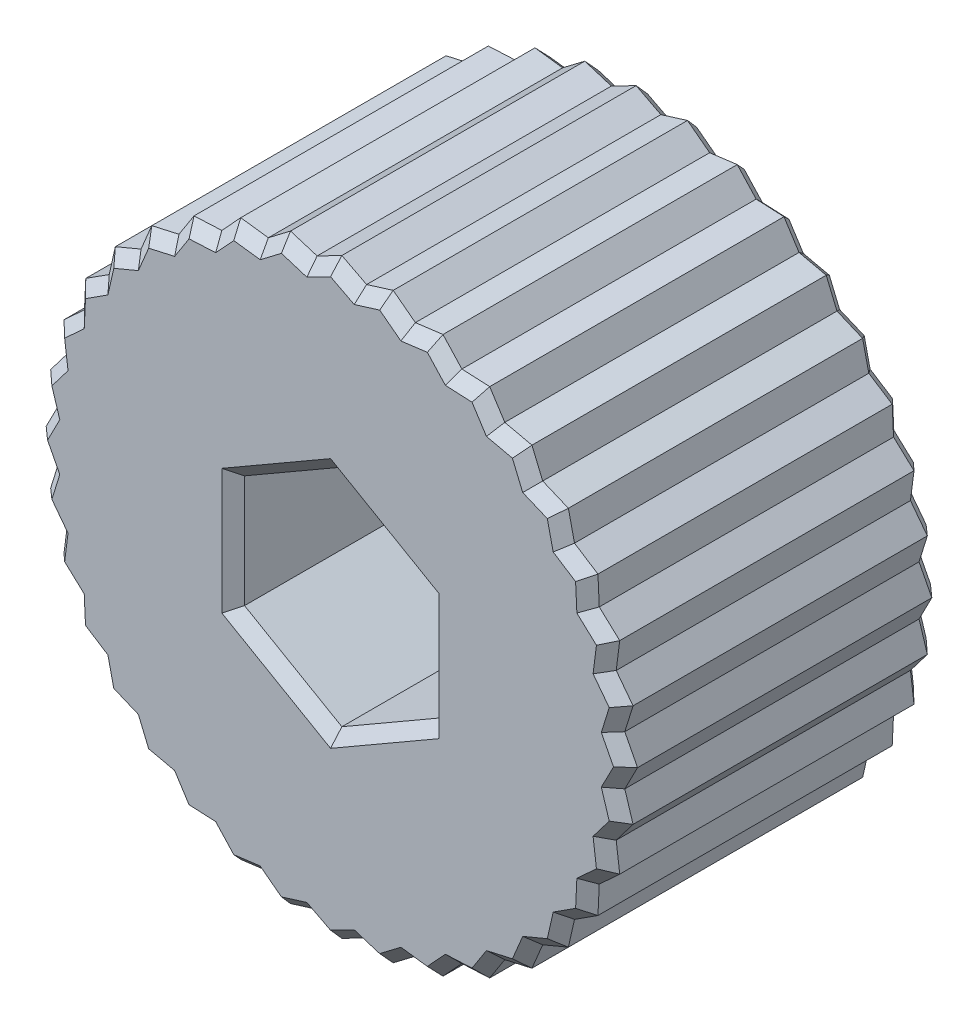
SolidWorks part; units mm, degrees
ref_plane "Front Plane (Z)" through (0, 0, 0) normal (0, 0, 1) x (1, 0, 0)
ref_plane "Top Plane (Y)" through (0, 0, 0) normal (0, 1, 0) x (1, 0, 0)
ref_plane "Side Plane (X)" through (0, 0, 0) normal (1, 0, 0) x (0, 0, -1)
sketch "Sketch1" plane through (0, 0, 0) normal (0, 0, 1) x (1, 0, 0)
  line L1 (0, 4.6765) -> (-4.05, 2.3383)
  line L2 (-4.05, 2.3383) -> (-4.05, -2.3383)
  line L3 (-4.05, -2.3383) -> (0, -4.6765)
  line L4 (0, -4.6765) -> (4.05, -2.3383)
  line L5 (4.05, -2.3383) -> (4.05, 2.3383)
  line L6 (4.05, 2.3383) -> (0, 4.6765)
  circle A1 centre (0, 0) radius 12.5
  circle A2 centre (0, 0) radius 4.05 construction
  dimension "D1" = 8.1
  dimension "D2" = 25
extrude "Boss-Extrude1" add sketch "Sketch1" along normal blind 14
sketch "Sketch3" plane through (0, 0, 0) normal (0, 0, -1) x (-1, 0, 0)
  circle A0 centre (0, 0) radius 2.9
  circle A1 centre (0, 0) radius 5.8015
  dimension "D1" = 5.8
extrude "Boss-Extrude3" add sketch "Sketch3" against normal blind 2
sketch "Sketch4" plane through (0, 0, 14) normal (0, 0, 1) x (1, 0, 0)
  line L0 (4.05, 2.3383) -> (4.05, -2.3383) construction
  line L1 (0, 4.9652) -> (-4.3, 2.4826)
  line L2 (-4.3, 2.4826) -> (-4.3, -2.4826)
  line L3 (-4.3, -2.4826) -> (0, -4.9652)
  line L4 (0, -4.9652) -> (4.3, -2.4826)
  line L5 (4.3, -2.4826) -> (4.3, 2.4826)
  line L6 (4.3, 2.4826) -> (0, 4.9652)
  circle A0 centre (0, 0) radius 4.3 construction
  dimension "D1" = 0.25
extrude "Cut-Extrude1" cut sketch "Sketch4" against normal offset from surface (7.5 mm away) 4.5 up to face at (0, 0, 2)
sketch "Sketch5" plane through (0, 0, 14) normal (0, 0, 1) x (1, 0, 0)
  line L0 (0, 0) -> (0, 15.5343) construction
  line L1 (0, 13.0632) -> (1.0936, 12.4995)
  line L2 (0, 0) -> (1.0936, 12.4995) construction
  line L3 (0, 13.0632) -> (-1.0936, 12.4995)
  line L4 (2.2684, 12.8647) -> (1.0936, 12.4995)
  line L5 (2.2684, 12.8647) -> (3.2475, 12.1197)
  line L6 (4.4679, 12.2754) -> (3.2475, 12.1197)
  line L7 (4.4679, 12.2754) -> (5.3027, 11.3716)
  line L8 (6.5316, 11.3131) -> (5.3027, 11.3716)
  line L9 (6.5316, 11.3131) -> (7.1968, 10.2781)
  line L10 (8.3969, 10.007) -> (7.1968, 10.2781)
  line L11 (8.3969, 10.007) -> (8.8722, 8.8722)
  line L12 (10.007, 8.3969) -> (8.8722, 8.8722)
  line L13 (10.007, 8.3969) -> (10.2781, 7.1968)
  line L14 (11.3131, 6.5316) -> (10.2781, 7.1968)
  line L15 (11.3131, 6.5316) -> (11.3716, 5.3027)
  line L16 (12.2754, 4.4679) -> (11.3716, 5.3027)
  line L17 (12.2754, 4.4679) -> (12.1197, 3.2475)
  line L18 (12.8647, 2.2684) -> (12.1197, 3.2475)
  line L19 (12.8647, 2.2684) -> (12.4995, 1.0936)
  line L20 (13.0632, 0) -> (12.4995, 1.0936)
  line L21 (13.0632, 0) -> (12.4995, -1.0936)
  line L22 (12.8647, -2.2684) -> (12.4995, -1.0936)
  line L23 (12.8647, -2.2684) -> (12.1197, -3.2475)
  line L24 (12.2754, -4.4679) -> (12.1197, -3.2475)
  line L25 (12.2754, -4.4679) -> (11.3716, -5.3027)
  line L26 (11.3131, -6.5316) -> (11.3716, -5.3027)
  line L27 (11.3131, -6.5316) -> (10.2781, -7.1968)
  line L28 (10.007, -8.3969) -> (10.2781, -7.1968)
  line L29 (10.007, -8.3969) -> (8.8722, -8.8722)
  line L30 (8.3969, -10.007) -> (8.8722, -8.8722)
  line L31 (8.3969, -10.007) -> (7.1968, -10.2781)
  line L32 (6.5316, -11.3131) -> (7.1968, -10.2781)
  line L33 (6.5316, -11.3131) -> (5.3027, -11.3716)
  line L34 (4.4679, -12.2754) -> (5.3027, -11.3716)
  line L35 (4.4679, -12.2754) -> (3.2475, -12.1197)
  line L36 (2.2684, -12.8647) -> (3.2475, -12.1197)
  line L37 (2.2684, -12.8647) -> (1.0936, -12.4995)
  line L38 (0, -13.0632) -> (1.0936, -12.4995)
  line L39 (0, -13.0632) -> (-1.0936, -12.4995)
  line L40 (-2.2684, -12.8647) -> (-1.0936, -12.4995)
  line L41 (-2.2684, -12.8647) -> (-3.2475, -12.1197)
  line L42 (-4.4679, -12.2754) -> (-3.2475, -12.1197)
  line L43 (-4.4679, -12.2754) -> (-5.3027, -11.3716)
  line L44 (-6.5316, -11.3131) -> (-5.3027, -11.3716)
  line L45 (-6.5316, -11.3131) -> (-7.1968, -10.2781)
  line L46 (-8.3969, -10.007) -> (-7.1968, -10.2781)
  line L47 (-8.3969, -10.007) -> (-8.8722, -8.8722)
  line L48 (-10.007, -8.3969) -> (-8.8722, -8.8722)
  line L49 (-10.007, -8.3969) -> (-10.2781, -7.1968)
  line L50 (-11.3131, -6.5316) -> (-10.2781, -7.1968)
  line L51 (-11.3131, -6.5316) -> (-11.3716, -5.3027)
  line L52 (-12.2754, -4.4679) -> (-11.3716, -5.3027)
  line L53 (-12.2754, -4.4679) -> (-12.1197, -3.2475)
  line L54 (-12.8647, -2.2684) -> (-12.1197, -3.2475)
  line L55 (-12.8647, -2.2684) -> (-12.4995, -1.0936)
  line L56 (-13.0632, 0) -> (-12.4995, -1.0936)
  line L57 (-13.0632, 0) -> (-12.4995, 1.0936)
  line L58 (-12.8647, 2.2684) -> (-12.4995, 1.0936)
  line L59 (-12.8647, 2.2684) -> (-12.1197, 3.2475)
  line L60 (-12.2754, 4.4679) -> (-12.1197, 3.2475)
  line L61 (-12.2754, 4.4679) -> (-11.3716, 5.3027)
  line L62 (-11.3131, 6.5316) -> (-11.3716, 5.3027)
  line L63 (-11.3131, 6.5316) -> (-10.2781, 7.1968)
  line L64 (-10.007, 8.3969) -> (-10.2781, 7.1968)
  line L65 (-10.007, 8.3969) -> (-8.8722, 8.8722)
  line L66 (-8.3969, 10.007) -> (-8.8722, 8.8722)
  line L67 (-8.3969, 10.007) -> (-7.1968, 10.2781)
  line L68 (-6.5316, 11.3131) -> (-7.1968, 10.2781)
  line L69 (-6.5316, 11.3131) -> (-5.3027, 11.3716)
  line L70 (-4.4679, 12.2754) -> (-5.3027, 11.3716)
  line L71 (-4.4679, 12.2754) -> (-3.2475, 12.1197)
  line L72 (-2.2684, 12.8647) -> (-3.2475, 12.1197)
  line L73 (-2.2684, 12.8647) -> (-1.0936, 12.4995)
  circle A1 centre (0, 0) radius 12.0902
  point P115 (0, 0)
  dimension "D2" = 36
extrude "Boss-Extrude4" add sketch "Sketch5" against normal up to surface (14 mm away) up to face at (12.5, 0, 0)
chamfer "Chamfer2" distance 0.5 angle 45 151 edges at (-2.9, 0, 0) (-4.3, 0, 14) (-2.15, -3.7239, 14) (2.15, -3.7239, 14) (4.3, 0, 14) (2.15, 3.7239, 14) (-2.15, 3.7239, 14) (-1.681, 12.6821, 0) (-1.681, 12.6821, 14) (-2.7579, 12.4922, 0) (-2.7579, 12.4922, 14) (-3.8577, 12.1975, 0) (-3.8577, 12.1975, 14) (-4.8853, 11.8235, 0) (-4.8853, 11.8235, 14) (-5.9171, 11.3424, 0) (-5.9171, 11.3424, 14) (-6.8642, 10.7956, 0) (-6.8642, 10.7956, 14) (-7.7968, 10.1425, 0) (-7.7968, 10.1425, 14) (-8.6345, 9.4396, 0) (-8.6345, 9.4396, 14) (-9.4396, 8.6345, 0) (-9.4396, 8.6345, 14) (-10.1425, 7.7968, 0) (-10.1425, 7.7968, 14) (-10.7956, 6.8642, 0) (-10.7956, 6.8642, 14) (-11.3424, 5.9171, 0) (-11.3424, 5.9171, 14) (-11.8235, 4.8853, 0) (-11.8235, 4.8853, 14) (-12.1975, 3.8577, 0) (-12.1975, 3.8577, 14) (-12.4922, 2.7579, 0) (-12.4922, 2.7579, 14) (-12.6821, 1.681, 0) (-12.6821, 1.681, 14) (-12.7813, 0.5468, 0) (-12.7813, 0.5468, 14) (-12.7813, -0.5468, 0) (-12.7813, -0.5468, 14) (-12.6821, -1.681, 0) (-12.6821, -1.681, 14) (-12.4922, -2.7579, 0) (-12.4922, -2.7579, 14) (-12.1975, -3.8577, 0) (-12.1975, -3.8577, 14) (-11.8235, -4.8853, 0) (-11.8235, -4.8853, 14) (-11.3424, -5.9171, 0) (-11.3424, -5.9171, 14) (-10.7956, -6.8642, 0) (-10.7956, -6.8642, 14) (-10.1425, -7.7968, 0) (-10.1425, -7.7968, 14) (-9.4396, -8.6345, 0) (-9.4396, -8.6345, 14) (-8.6345, -9.4396, 0) (-8.6345, -9.4396, 14) (-7.7968, -10.1425, 0) (-7.7968, -10.1425, 14) (-6.8642, -10.7956, 0) (-6.8642, -10.7956, 14) (-5.9171, -11.3424, 0) (-5.9171, -11.3424, 14) (-4.8853, -11.8235, 0) (-4.8853, -11.8235, 14) (-3.8577, -12.1975, 0) (-3.8577, -12.1975, 14) (-2.7579, -12.4922, 0) (-2.7579, -12.4922, 14) (-1.681, -12.6821, 0) (-1.681, -12.6821, 14) (-0.5468, -12.7813, 0) (-0.5468, -12.7813, 14) (0.5468, -12.7813, 0) (0.5468, -12.7813, 14) (1.681, -12.6821, 0) (1.681, -12.6821, 14) (2.7579, -12.4922, 0) (2.7579, -12.4922, 14) (3.8577, -12.1975, 0) (3.8577, -12.1975, 14) (4.8853, -11.8235, 0) (4.8853, -11.8235, 14) (5.9171, -11.3424, 0) (5.9171, -11.3424, 14) (6.8642, -10.7956, 0) (6.8642, -10.7956, 14) (7.7968, -10.1425, 0) (7.7968, -10.1425, 14) (8.6345, -9.4396, 0) (8.6345, -9.4396, 14) (9.4396, -8.6345, 0) (9.4396, -8.6345, 14) (10.1425, -7.7968, 0) (10.1425, -7.7968, 14) (10.7956, -6.8642, 0) (10.7956, -6.8642, 14) (11.3424, -5.9171, 0) (11.3424, -5.9171, 14) (11.8235, -4.8853, 0) (11.8235, -4.8853, 14) (12.1975, -3.8577, 0) (12.1975, -3.8577, 14) (12.4922, -2.7579, 0) (12.4922, -2.7579, 14) (12.6821, -1.681, 0) (12.6821, -1.681, 14) (12.7813, -0.5468, 0) (12.7813, -0.5468, 14) (12.7813, 0.5468, 0) (12.7813, 0.5468, 14) (12.6821, 1.681, 0) (12.6821, 1.681, 14) (12.4922, 2.7579, 0) (12.4922, 2.7579, 14) (12.1975, 3.8577, 0) (12.1975, 3.8577, 14) (11.8235, 4.8853, 0) (11.8235, 4.8853, 14) (11.3424, 5.9171, 0) (11.3424, 5.9171, 14) (10.7956, 6.8642, 0) (10.7956, 6.8642, 14) (10.1425, 7.7968, 0) (10.1425, 7.7968, 14) (9.4396, 8.6345, 0) (9.4396, 8.6345, 14) (8.6345, 9.4396, 0) (8.6345, 9.4396, 14) (7.7968, 10.1425, 0) (7.7968, 10.1425, 14) (6.8642, 10.7956, 0) (6.8642, 10.7956, 14) (5.9171, 11.3424, 0) (5.9171, 11.3424, 14) (4.8853, 11.8235, 0) (4.8853, 11.8235, 14) (3.8577, 12.1975, 0) (3.8577, 12.1975, 14) (2.7579, 12.4922, 0) (2.7579, 12.4922, 14) (1.681, 12.6821, 0) (1.681, 12.6821, 14) (0.5468, 12.7813, 0) (0.5468, 12.7813, 14) (-0.5468, 12.7813, 0) (-0.5468, 12.7813, 14)
